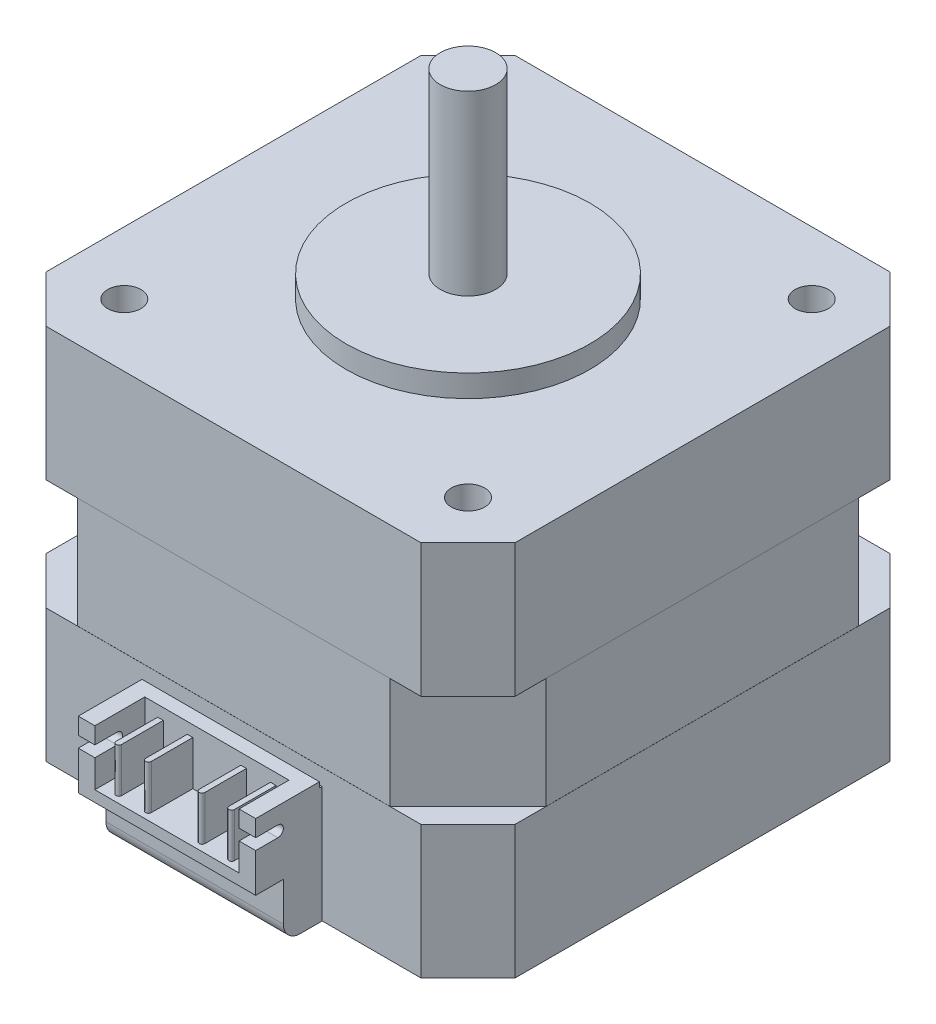
SolidWorks part; units mm, degrees
material "1060 Alloy"
ref_plane "Front Plane" through (0, 0, 0) normal (0, 0, 1) x (1, 0, 0)
ref_plane "Top Plane" through (0, 0, 0) normal (0, 1, 0) x (1, 0, 0)
ref_plane "Right Plane" through (0, 0, 0) normal (1, 0, 0) x (0, 0, -1)
sketch "Sketch1" plane through (0, 0, 0) normal (0, 1, 0) x (1, 0, 0)
  line L9 (-21.15, -21.15) -> (21.15, -21.15)
  line L10 (-21.15, -21.15) -> (-21.15, 21.15)
  line L11 (-21.15, 21.15) -> (21.15, 21.15)
  line L12 (21.15, -21.15) -> (21.15, 21.15)
  line L13 (-21.15, -21.15) -> (21.15, 21.15) construction
  line L14 (-21.15, 21.15) -> (21.15, -21.15) construction
  point P0 (0, 0)
  dimension "D1" = 42.3
extrude "Boss-Extrude1" add sketch "Sketch1" along normal blind 34
sketch "Sketch2" plane through (0, 34, 0) normal (0, 1, 0) x (1, 0, 0)
  circle A0 centre (0, 0) radius 11
  dimension "D1" = 22
extrude "Boss-Extrude2" add sketch "Sketch2" along normal blind 2
sketch "Sketch3" plane through (0, 36, 0) normal (0, 1, 0) x (1, 0, 0)
  circle A0 centre (0, 0) radius 2.5
  dimension "D1" = 5
extrude "Boss-Extrude3" add sketch "Sketch3" along normal blind 16
sketch "Sketch4" plane through (0, 34, 0) normal (0, 1, 0) x (1, 0, 0)
  line L0 (-21.15, 16.9074) -> (-16.9074, 21.15)
  line L1 (-21.15, 21.15) -> (-21.15, -21.15) construction
  line L2 (21.15, 21.15) -> (-21.15, 21.15) construction
  line L3 (-16.9074, 21.15) -> (-21.15, 21.15)
  line L4 (-21.15, 21.15) -> (-21.15, 16.9074)
  line L5 (0, 0) -> (0, 27.6659) construction
  line L6 (21.15, 21.15) -> (21.15, 16.9074)
  line L7 (16.9074, 21.15) -> (21.15, 21.15)
  line L8 (21.15, 16.9074) -> (16.9074, 21.15)
  line L9 (0, 0) -> (-36.313, 0) construction
  line L10 (21.15, -16.9074) -> (16.9074, -21.15)
  line L11 (16.9074, -21.15) -> (21.15, -21.15)
  line L12 (21.15, -21.15) -> (21.15, -16.9074)
  line L13 (-21.15, -21.15) -> (-21.15, -16.9074)
  line L14 (-16.9074, -21.15) -> (-21.15, -21.15)
  line L15 (-21.15, -16.9074) -> (-16.9074, -21.15)
  dimension "D1" = 45
  dimension "D2" = 6
extrude "Cut-Extrude1" cut sketch "Sketch4" against normal through all both and the other way through all
sketch "Sketch5" plane through (21.15, 0, 0) normal (1, 0, 0) x (0, 0, -1)
  line L0 (-16.9074, 0) -> (-16.9074, 34) construction
  line L1 (16.9074, 12) -> (-16.9074, 12)
  line L2 (16.9074, 12) -> (16.9074, 22)
  line L3 (16.9074, 22) -> (-16.9074, 22)
  line L4 (-16.9074, 12) -> (-16.9074, 22)
  line L5 (16.9074, 12) -> (-16.9074, 22) construction
  line L6 (16.9074, 22) -> (-16.9074, 12) construction
  line L7 (-16.9074, 0) -> (16.9074, 0) construction
  line L8 (-16.9074, 34) -> (16.9074, 34) construction
  line L9 (16.9074, 0) -> (16.9074, 34) construction
  point P0 (0, 17)
  dimension "D1" = 12
  dimension "D2" = 12
extrude "Cut-Extrude2" cut sketch "Sketch5" against normal blind 0.01
sketch "Sketch6" plane through (0, 34, 0) normal (0, 1, 0) x (1, 0, 0)
  line L0 (21.15, 14.0789) -> (14.0789, 21.15)
  line L1 (21.15, -16.9074) -> (21.15, 16.9074) construction
  line L2 (16.9074, 21.15) -> (-16.9074, 21.15) construction
  line L3 (14.0789, 21.15) -> (21.15, 21.15)
  line L4 (21.15, 21.15) -> (21.15, 14.0789)
  dimension "D1" = 10
  dimension "D2" = 45
extrude "Cut-Extrude3" cut sketch "Sketch6" against normal up to surface (10 mm away) from surface at -12 up to face at (21.145, 12, 0) starting at face at (21.145, 22, 0)
pattern_circular "CirPattern1" count 4 over 360 about axis through (0, 0, 0) along (0, 1, 0) of "Cut-Extrude2", "Cut-Extrude3"
sketch "Sketch7" plane through (0, 34, 0) normal (0, 1, 0) x (1, 0, 0)
  circle A0 centre (15.5, 15.5) radius 1.5
  circle A1 centre (15.5, -15.5) radius 1.5
  circle A2 centre (-15.5, -15.5) radius 1.5
  circle A3 centre (-15.5, 15.5) radius 1.5
  point P12 (0, 0)
  dimension "D3" = 3
  dimension "D5" = 31
  dimension "D1" = 15.5
  dimension "D2" = 15.5
  dimension "D4" = 4
extrude "Cut-Extrude4" cut sketch "Sketch7" against normal blind 4.5
sketch "Sketch8" plane through (0, 0, 21.15) normal (0, 0, 1) x (1, 0, 0)
  line L0 (-16.9074, 0) -> (16.9074, 0) construction
  line L1 (-8, 0) -> (8, 0)
  line L2 (-8, 0) -> (-8, 11)
  line L3 (-8, 11) -> (8, 11)
  line L4 (8, 0) -> (8, 11)
  dimension "D1" = 16
  dimension "D2" = 11
extrude "Boss-Extrude4" add sketch "Sketch8" along normal blind 6
sketch "Sketch9" plane through (0, 0, 27.15) normal (0, 0, 1) x (1, 0, 0)
  line L0 (8, 0) -> (8, 11) construction
  line L1 (-8, 0) -> (8, 0)
  line L2 (-8, 0) -> (-8, 5)
  line L3 (-8, 5) -> (8, 5)
  line L4 (8, 0) -> (8, 5)
  dimension "D1" = 5
extrude "Cut-Extrude5" cut sketch "Sketch9" against normal blind 2.5
fillet "Fillet1" radius 1.5 1 edges at (0, 0, 24.65)
sketch "Sketch10" plane through (0, 11, 0) normal (0, 1, 0) x (1, 0, 0)
  line L0 (8, -27.15) -> (-8, -27.15) construction
  line L1 (-6.5, -27.15) -> (6.5, -27.15)
  line L2 (-6.5, -27.15) -> (-6.5, -22.65)
  line L3 (-6.5, -22.65) -> (6.5, -22.65)
  line L4 (6.5, -27.15) -> (6.5, -22.65)
  point P6 (0, -27.15)
  dimension "D1" = 13
  dimension "D2" = 4.5
extrude "Cut-Extrude6" cut sketch "Sketch10" against normal blind 5
sketch "Sketch11" plane through (8, 0, 0) normal (1, 0, 0) x (0, 0, -1)
  line L0 (-27.15, 5) -> (-27.15, 11) construction
  line L1 (-27.15, 11) -> (-21.15, 11) construction
  line L2 (-27.15, 9.5) -> (-25.15, 9.5)
  line L3 (-27.15, 9.5) -> (-27.15, 8.5)
  line L4 (-27.15, 8.5) -> (-25.15, 8.5)
  arc A0 (-25.15, 8.5) -> (-25.15, 9.5) centre (-25.15, 9) ccw
  point P5 (-24.65, 9)
  dimension "D2" = 1.5
  dimension "D1" = 1
extrude "Cut-Extrude7" cut sketch "Sketch11" against normal through all
sketch "Sketch12" plane through (0, 6, 0) normal (0, 1, 0) x (1, 0, 0)
  line L0 (0, 5.4741) -> (0, -32.9784) construction
  line L1 (6.5, -22.65) -> (-6.5, -22.65) construction
  line L2 (-2.667, -22.65) -> (-2.167, -22.65)
  line L3 (-2.667, -22.65) -> (-2.667, -26.4)
  line L5 (-2.167, -22.65) -> (-2.167, -26.4)
  line L8 (5.334, -22.65) -> (5.334, -26.4)
  line L9 (-4.834, -22.65) -> (-5.334, -22.65)
  line L10 (-4.834, -22.65) -> (-4.834, -26.4)
  line L12 (-5.334, -22.65) -> (-5.334, -26.4)
  line L13 (4.834, -22.65) -> (4.834, -26.4)
  line L14 (4.834, -22.65) -> (5.334, -22.65)
  line L15 (2.167, -22.65) -> (2.167, -26.4)
  line L16 (2.667, -22.65) -> (2.667, -26.4)
  line L17 (2.667, -22.65) -> (2.167, -22.65)
  arc A0 (-5.334, -26.4) -> (-4.834, -26.4) centre (-5.084, -26.4) ccw
  arc A1 (-2.667, -26.4) -> (-2.167, -26.4) centre (-2.417, -26.4) ccw
  arc A2 (2.667, -26.4) -> (2.167, -26.4) centre (2.417, -26.4) cw
  arc A3 (5.334, -26.4) -> (4.834, -26.4) centre (5.084, -26.4) cw
  point P4 (-2.417, -26.65)
  point P11 (-5.084, -26.65)
  dimension "D7" = 0.25
  dimension "D1" = 0.25
  dimension "D2" = 0.5
  dimension "D3" = 2.167
  dimension "D4" = 4
  dimension "D5" = 0.5
  dimension "D6" = 2.167
  dimension "D8" = 4
extrude "Boss-Extrude5" add sketch "Sketch12" along normal blind 4
sketch "Sketch13" plane through (0, 11, 0) normal (0, 1, 0) x (1, 0, 0)
  line L0 (8, -27.15) -> (8, -21.15) construction
  line L1 (-8, -21.15) -> (8, -21.15)
  line L2 (-8, -21.15) -> (-8, -21.4)
  line L3 (-8, -21.4) -> (8, -21.4)
  line L4 (8, -21.15) -> (8, -21.4)
  dimension "D1" = 0.25
extrude "Cut-Extrude8" cut sketch "Sketch13" against normal blind 0.5
fillet "Fillet2" radius 0.125 1 edges at (0, 10.5, 21.4)
